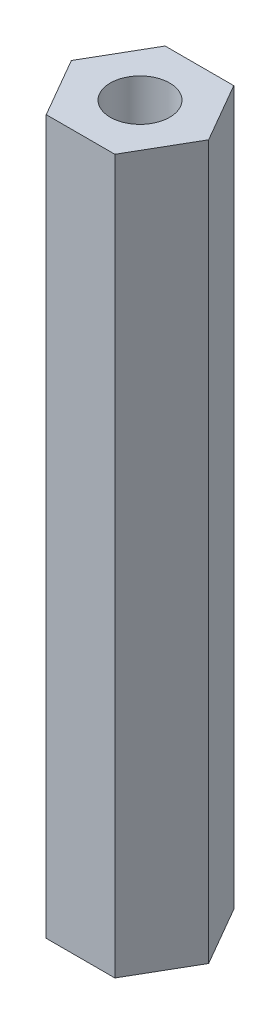
SolidWorks part; units mm, degrees
material "6061-T6 (SS)"
ref_plane "Front Plane" through (0, 0, 0) normal (0, 0, 1) x (1, 0, 0)
ref_plane "Top Plane" through (0, 0, 0) normal (0, 1, 0) x (1, 0, 0)
ref_plane "Right Plane" through (0, 0, 0) normal (1, 0, 0) x (0, 0, -1)
sketch "Sketch1" plane through (0, 0, 0) normal (0, 1, 0) x (1, 0, 0)
  line L1 (3.6662, -6.35) -> (7.3323, 0)
  line L2 (7.3323, 0) -> (3.6662, 6.35)
  line L3 (3.6662, 6.35) -> (-3.6662, 6.35)
  line L4 (-3.6662, 6.35) -> (-7.3323, 0)
  line L5 (-7.3323, 0) -> (-3.6662, -6.35)
  line L6 (-3.6662, -6.35) -> (3.6662, -6.35)
  circle A0 centre (0, 0) radius 6.35 construction
  circle A1 centre (0, 0) radius 3.175
  point P10 (-5.4993, -3.175)
  point P11 (5.4993, 3.175)
  dimension "D2" = 6.35
  dimension "D1" = 12.7
extrude "Boss-Extrude1" add sketch "Sketch1" along normal mid plane 76.2
